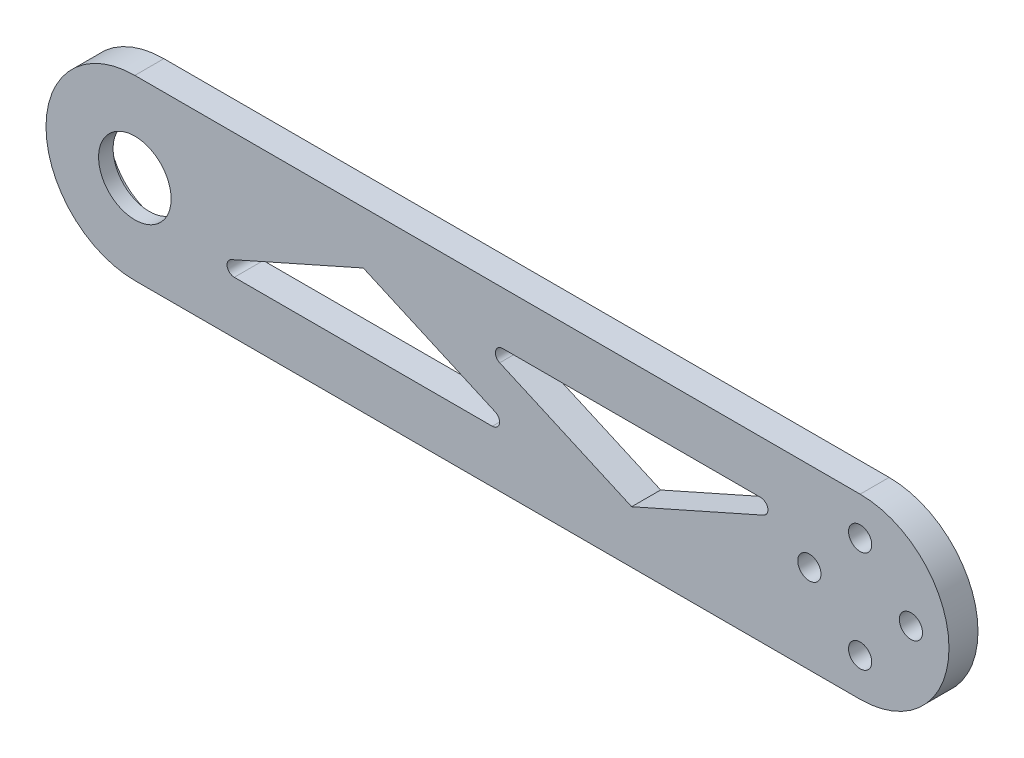
SolidWorks part; units mm, degrees
ref_plane "前视基准面" through (0, 0, 0) normal (0, 0, 1) x (1, 0, 0)
ref_plane "上视基准面" through (0, 0, 0) normal (0, 1, 0) x (1, 0, 0)
ref_plane "右视基准面" through (0, 0, 0) normal (1, 0, 0) x (0, 0, -1)
sketch "草图1" plane through (0, 0, 0) normal (0, 0, 1) x (1, 0, 0)
  line L0 (0, 12.25) -> (100, 12.25)
  line L1 (0, -12.25) -> (100, -12.25)
  arc A0 (0, 12.25) -> (0, -12.25) centre (0, 0) ccw
  arc A1 (100, -12.25) -> (100, 12.25) centre (100, 0) ccw
  circle A2 centre (0, 0) radius 5
  circle A9 centre (100, 7) radius 1.6
  circle A10 centre (107, 0) radius 1.6
  circle A11 centre (100, -7) radius 1.6
  circle A12 centre (93, 0) radius 1.6
  point P20 (100, 0)
  point P29 (100, 0)
  dimension "D1" = 24.5
  dimension "D3" = 10
  dimension "D7" = 3.2
  dimension "D4" = 100
  dimension "D2" = 2
extrude "凸台-拉伸1" add sketch "草图1" along normal blind 4
ref_plane "基准面6" through (0, 0, 2) normal (0, 0, 1) x (1, 0, 0)
sketch "草图4" plane through (0, 0, 2) normal (0, 0, 1) x (1, 0, 0)
  circle A0 centre (0, 0) radius 7.5
  dimension "D1" = 15
extrude "切除-拉伸3" cut sketch "草图4" against normal blind 3
sketch "草图5" plane through (0, 0, 4) normal (0, 0, 1) x (1, 0, 0)
  line L0 (0, 0) -> (124.3617, 0) construction
  line L1 (5, 5) -> (50, 5) construction
  line L2 (0, -5) -> (114.8619, -5) construction
  line L23 (50, 12.25) -> (50, -21.3969) construction
  line L24 (100, 12.25) -> (0, 12.25) construction
  line L25 (5, 0) -> (5, 8.1706) construction
  line L26 (91.3916, 0) -> (91.3916, 9.507) construction
  line L27 (27.5, 5) -> (27.5, -5) construction
  line L38 (31.5, 5) -> (13.3061, -3.0862)
  line L39 (13.7122, -5) -> (49.2878, -5)
  line L40 (49.6939, -3.0862) -> (31.5, 5)
  line L44 (68.5, -5) -> (86.6939, 3.0862)
  line L45 (50.3061, 3.0862) -> (68.5, -5)
  line L46 (86.2878, 5) -> (50.7122, 5)
  circle A8 centre (0, 0) radius 5 construction
  arc A9 (86.2878, 5) -> (86.6939, 3.0862) centre (86.2878, 4) cw
  arc A10 (50.7122, 5) -> (50.3061, 3.0862) centre (50.7122, 4) ccw
  arc A11 (49.2878, -5) -> (49.6939, -3.0862) centre (49.2878, -4) ccw
  arc A12 (13.3061, -3.0862) -> (13.7122, -5) centre (13.7122, -4) ccw
  dimension "D1" = 1
extrude "切除-拉伸4" cut sketch "草图5" against normal up to next
